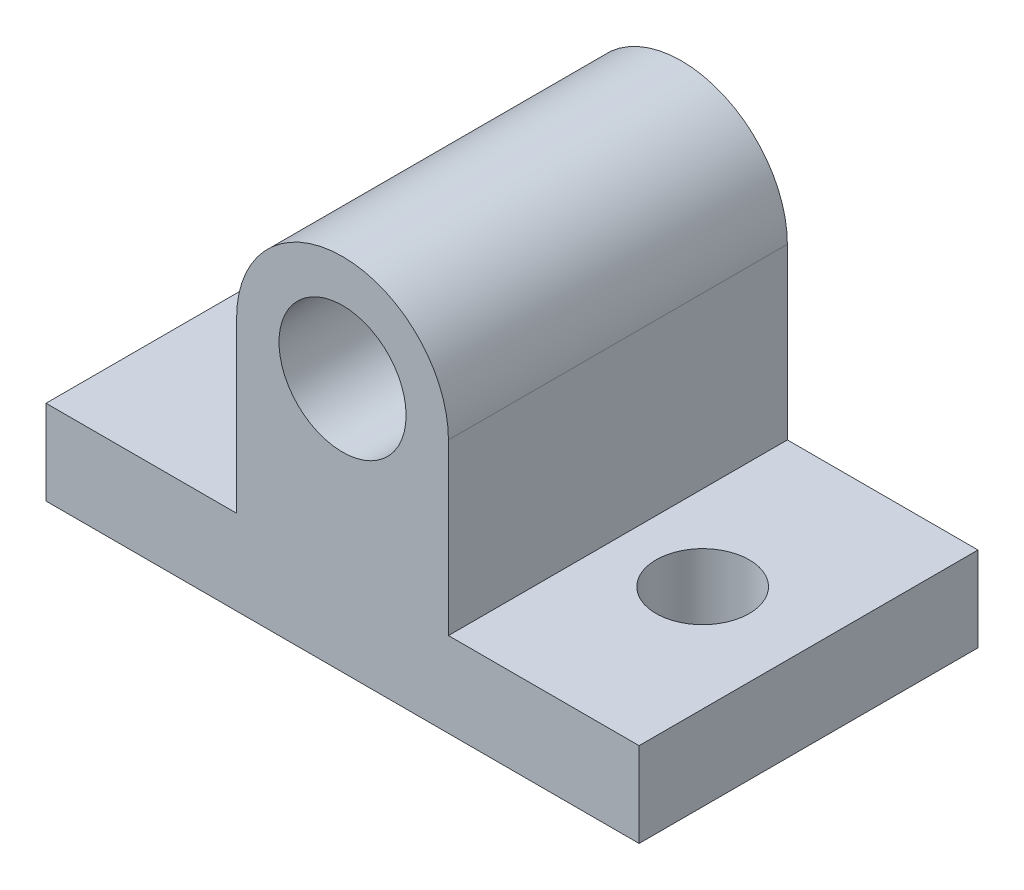
SolidWorks part; units mm, degrees
ref_plane "Front Plane" through (0, 0, 0) normal (0, 0, 1) x (1, 0, 0)
ref_plane "Top Plane" through (0, 0, 0) normal (0, 1, 0) x (1, 0, 0)
ref_plane "Right Plane" through (0, 0, 0) normal (1, 0, 0) x (0, 0, -1)
sketch "Base Sketch" plane through (0, 0, 0) normal (0, 1, 0) x (1, 0, 0)
  line L1 (-7, -4) -> (7, -4)
  line L2 (-7, -4) -> (-7, 4)
  line L3 (-7, 4) -> (7, 4)
  line L4 (7, -4) -> (7, 4)
  line L5 (-7, -4) -> (7, 4) construction
  line L6 (-7, 4) -> (7, -4) construction
  point P0 (0, 0)
  dimension "D1" = 14
  dimension "D2" = 8
extrude "Base Extrude" add sketch "Base Sketch" along normal blind 2
sketch "Protrusion Sketch" plane through (0, 0, 0) normal (0, 0, 1) x (1, 0, 0)
  line L0 (-7, 2) -> (7, 2) construction
  line L1 (-2.5, 2) -> (2.5, 2)
  line L2 (-2.5, 2) -> (-2.5, 6)
  line L3 (-2.5, 6) -> (2.5, 6)
  line L4 (2.5, 2) -> (2.5, 6)
  arc A0 (-2.5, 6) -> (2.5, 6) centre (0, 6) cw
  point P7 (0, 8.5)
  dimension "D1" = 2.5
  dimension "D2" = 4
extrude "Protrusion Extrude" add sketch "Protrusion Sketch" along normal up to surface and the other way up to surface contours A0 L3 | L1 L4 L3 L2 up to face at (0, 1, 4) other way up to face at (0, 1, -4)
sketch "Hole Locations Top Plane" plane through (0, 0, 0) normal (0, 1, 0) x (1, 0, 0)
  point P0 (0, 0)
  point P1 (4.5, 0)
  point P3 (-4.5, 0)
  dimension "D1" = 4.5
  dimension "D2" = 9
sketch "Hole Location Front Plane" plane through (0, 0, 0) normal (0, 0, 1) x (1, 0, 0)
  point P0 (0, 6)
hole_wizard "Ø3.0 (3) Diameter Hole1" positions "Sketch5" profile "Sketch6" hole size "Ø3.0" standard "ANSI Metric" end condition through all
sketch "Sketch5" plane through (0, 0, 4) normal (0, 0, 1) x (1, 0, 0)
  point P0 (0, 6)
sketch "Sketch6" plane through (0, 6, 4) normal (1, 0, 0) x (0, -1, 0)
  line L0 (0, 0) -> (0, 8)
  line L1 (0, 8) -> (1.5, 8)
  line L2 (1.5, 8) -> (1.5, 0)
  line L5 (1.5, 0) -> (0, 0)
  line L11 (0, -6.35) -> (0, 107.95) construction
  dimension "Thru Hole Dia." = 3
  dimension "Thru Hole Depth" = 8
hole_wizard "Ø2.2 (2.2) Diameter Hole1" positions "Sketch7" profile "Sketch8" hole size "Ø2.2" standard "ANSI Metric" end condition through all
sketch "Sketch7" plane through (0, 0, 0) normal (0, -1, 0) x (-1, 0, 0)
  point P0 (4.5, 0)
  point P3 (-4.5, 0)
sketch "Sketch8" plane through (-4.5, 0, 0) normal (1, 0, 0) x (0, 0, -1)
  line L0 (0, 0) -> (0, 8.5)
  line L1 (0, 8.5) -> (1.1, 8.5)
  line L2 (1.1, 8.5) -> (1.1, 0)
  line L5 (1.1, 0) -> (0, 0)
  line L11 (0, -6.35) -> (0, 107.95) construction
  dimension "Thru Hole Dia." = 2.2
  dimension "Thru Hole Depth" = 8.5
hole_wizard "Ø3.0 (3) Diameter Hole2" positions "Sketch9" profile "Sketch11" hole size "Ø3.0" standard "ANSI Metric"
sketch "Sketch9" plane through (0, 0, 0) normal (0, -1, 0) x (-1, 0, 0)
  point P0 (0, 0)
sketch "Sketch11" plane through (0, 0, 0) normal (1, 0, 0) x (0, 0, -1)
  line L0 (0, 0) -> (0, 6.9013)
  line L1 (0, 6.9013) -> (1.5, 6)
  line L2 (1.5, 6) -> (1.5, 0)
  line L5 (1.5, 0) -> (0, 0)
  line L10 (0, 6.9013) -> (-1.5, 6) construction
  line L11 (0, -6.35) -> (0, 107.95) construction
  dimension "Hole Dia." = 3
  dimension "Hole Depth" = 6
  dimension "Drill Angle" = 118
sketch "5mm Cut Sketch" plane through (0, 0, 0) normal (0, 1, 0) x (1, 0, 0)
  circle A0 centre (0, 0) radius 2.5
  dimension "D1" = 5
extrude "5 mm diameter Cut" cut sketch "5mm Cut Sketch" along normal blind 0.7 from surface at 0 starting at face at (0, 0, -1.5)
